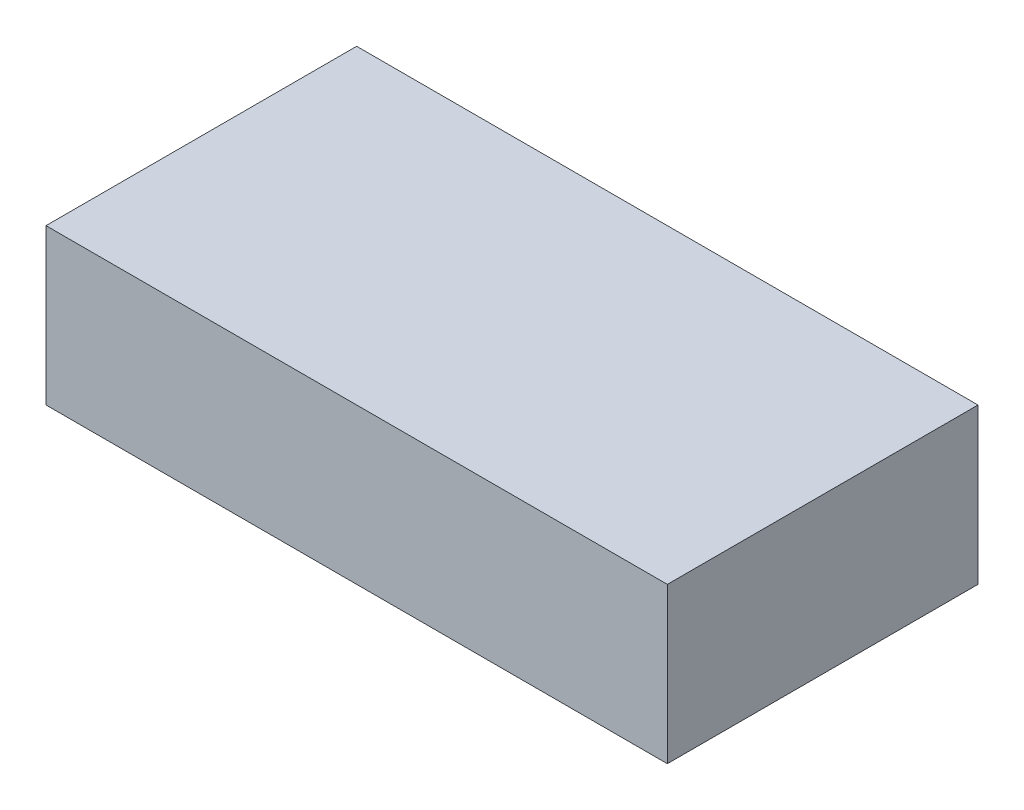
SolidWorks part; units mm, degrees
ref_plane "Front" through (0, 0, 0) normal (0, 0, 1) x (1, 0, 0)
ref_plane "Top" through (0, 0, 0) normal (0, 1, 0) x (1, 0, 0)
ref_plane "Right" through (0, 0, 0) normal (1, 0, 0) x (0, 0, -1)
sketch "Sketch1" plane through (0, 0, 0) normal (0, 1, 0) x (1, 0, 0)
  line L1 (-100, 50) -> (100, 50)
  line L2 (-100, 50) -> (-100, -50)
  line L3 (-100, -50) -> (100, -50)
  line L4 (100, 50) -> (100, -50)
  line L5 (-100, 50) -> (100, -50) construction
  line L6 (-100, -50) -> (100, 50) construction
  point P0 (0, 0)
  dimension "D1" = 200
  dimension "D2" = 100
extrude "Boss-Extrude1" add sketch "Sketch1" along normal mid plane 50
sketch "Sketch2" plane through (-100, 0, 0) normal (-1, 0, 0) x (0, 0, 1)
  line L0 (-50, 25) -> (50, 25) construction
  line L1 (25, 25) -> (-50, 25)
  line L2 (25, 25) -> (25, 0)
  line L3 (25, 0) -> (-50, 0)
  line L4 (-50, 25) -> (-50, 0)
  line L5 (-50, 25) -> (-50, -25) construction
  line L6 (50, 25) -> (50, -25) construction
  dimension "D1" = 25
  dimension "D2" = 25
